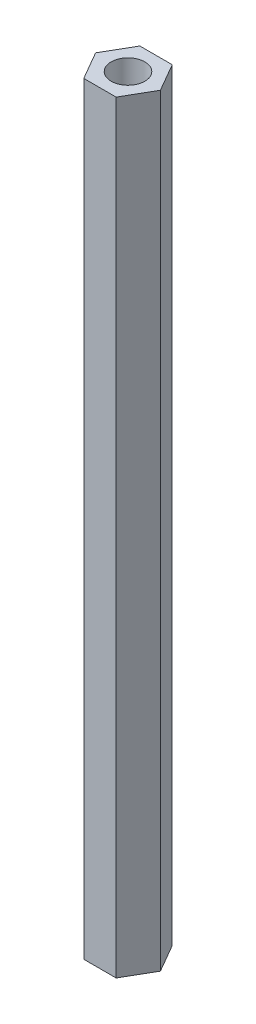
SolidWorks part; units mm, degrees
ref_plane "Front" through (0, 0, 0) normal (0, 0, 1) x (1, 0, 0)
ref_plane "Top" through (0, 0, 0) normal (0, 1, 0) x (1, 0, 0)
ref_plane "Right" through (0, 0, 0) normal (1, 0, 0) x (0, 0, -1)
sketch "草图1" plane through (0, 0, 0) normal (0, 1, 0) x (1, 0, 0)
  line L1 (2.8868, 0) -> (1.4434, 2.5)
  line L2 (1.4434, 2.5) -> (-1.4434, 2.5)
  line L3 (-1.4434, 2.5) -> (-2.8868, 0)
  line L4 (-2.8868, 0) -> (-1.4434, -2.5)
  line L5 (-1.4434, -2.5) -> (1.4434, -2.5)
  line L6 (1.4434, -2.5) -> (2.8868, 0)
  circle A0 centre (0, 0) radius 2.5 construction
  dimension "D1" = 5
extrude "凸台-拉伸1" add sketch "草图1" along normal blind 68
sketch "草图2" plane through (0, 68, 0) normal (0, 1, 0) x (1, 0, 0)
  circle A0 centre (0, 0) radius 1.5
  dimension "D1" = 3
extrude "切除-拉伸1" cut sketch "草图2" against normal through all
